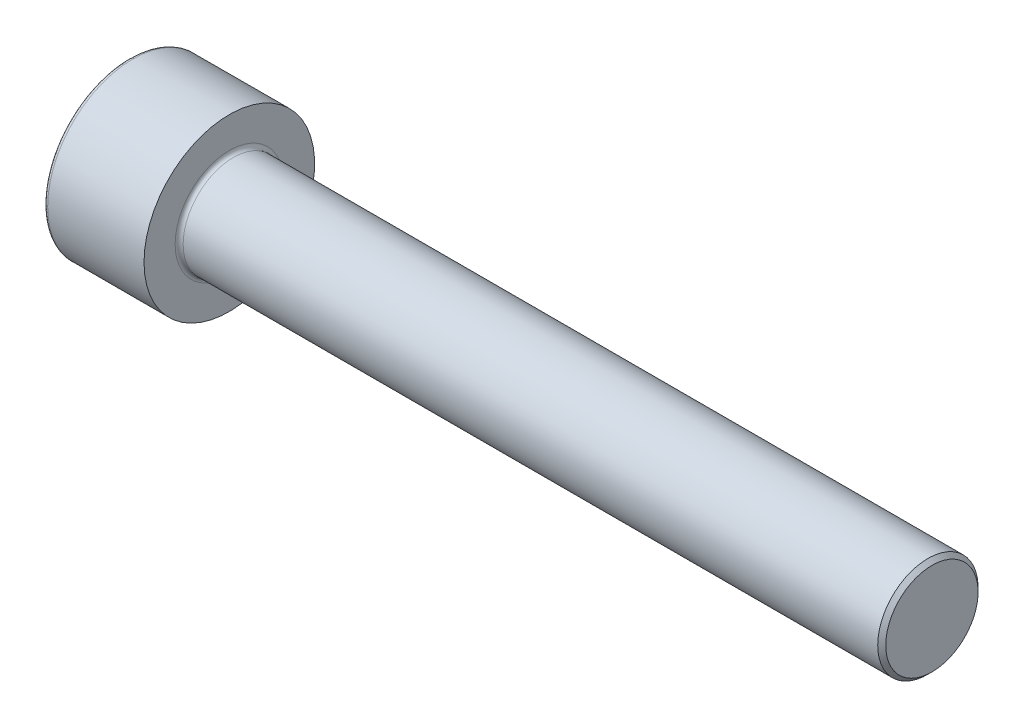
SolidWorks part; units mm, degrees
ref_plane "Front Plane" through (0, 0, 0) normal (0, 0, 1) x (1, 0, 0)
ref_plane "Top Plane" through (0, 0, 0) normal (0, 1, 0) x (1, 0, 0)
ref_plane "Right Plane" through (0, 0, 0) normal (1, 0, 0) x (0, 0, -1)
sketch "草图1" plane through (0, 0, 0) normal (0, 0, 1) x (1, 0, 0)
  line L0 (0, 0) -> (32.2917, 0) construction
  line L1 (0, 0) -> (0, 4.25)
  line L2 (0, 4.25) -> (5, 4.25)
  line L3 (5, 4.25) -> (5, 2.5)
  line L4 (5, 2.5) -> (40, 2.5)
  line L5 (40, 2.5) -> (40, 0)
  line L6 (40, 0) -> (0, 0)
  dimension "D1" = 5
  dimension "D2" = 8.5
  dimension "D3" = 5
  dimension "D4" = 35
revolve "旋转1" add sketch "草图1" angle 360 about L0
chamfer "倒角1" distance 0.2 angle 45 1 edges at (40, 0, 2.5)
fillet "圆角1" radius 0.2 1 edges at (0, 0, 4.25)
hole_wizard "Ø4.0 (4) 直径孔1" positions "草图4" profile "草图3" hole size "Ø4.0" standard "GB"
sketch "草图4" plane through (0, 0, 0) normal (-1, 0, 0) x (0, 0, 1)
  point P0 (0, 0)
sketch "草图3" plane through (0, 0, 0) normal (0, 1, 0) x (0, 0, 1)
  line L0 (0, 0) -> (0, 3.7017)
  line L1 (0, 3.7017) -> (2, 2.5)
  line L2 (2, 2.5) -> (2, 0)
  line L5 (2, 0) -> (0, 0)
  line L10 (0, 3.7017) -> (-2, 2.5) construction
  line L11 (0, -6.35) -> (0, 107.95) construction
  dimension "孔直径" = 4
  dimension "孔深度" = 2.5
  dimension "导头角度" = 118
sketch "草图2" plane through (0, 0, 0) normal (-1, 0, 0) x (0, 0, 1)
  line L0 (0, 4.05) -> (0, -4.05) construction
  line L1 (0, -2.3094) -> (2, -1.1547)
  line L2 (2, -1.1547) -> (2, 1.1547)
  line L3 (2, 1.1547) -> (0, 2.3094)
  line L4 (0, 2.3094) -> (-2, 1.1547)
  line L5 (-2, 1.1547) -> (-2, -1.1547)
  line L6 (-2, -1.1547) -> (0, -2.3094)
  circle A0 centre (0, 0) radius 2 construction
  circle A1 centre (0, 0) radius 4.05 construction
  dimension "D1" = 4
extrude "切除-拉伸1" cut sketch "草图2" against normal blind 2.5
fillet "圆角2" radius 0.2 1 edges at (5, 0, 2.5)
